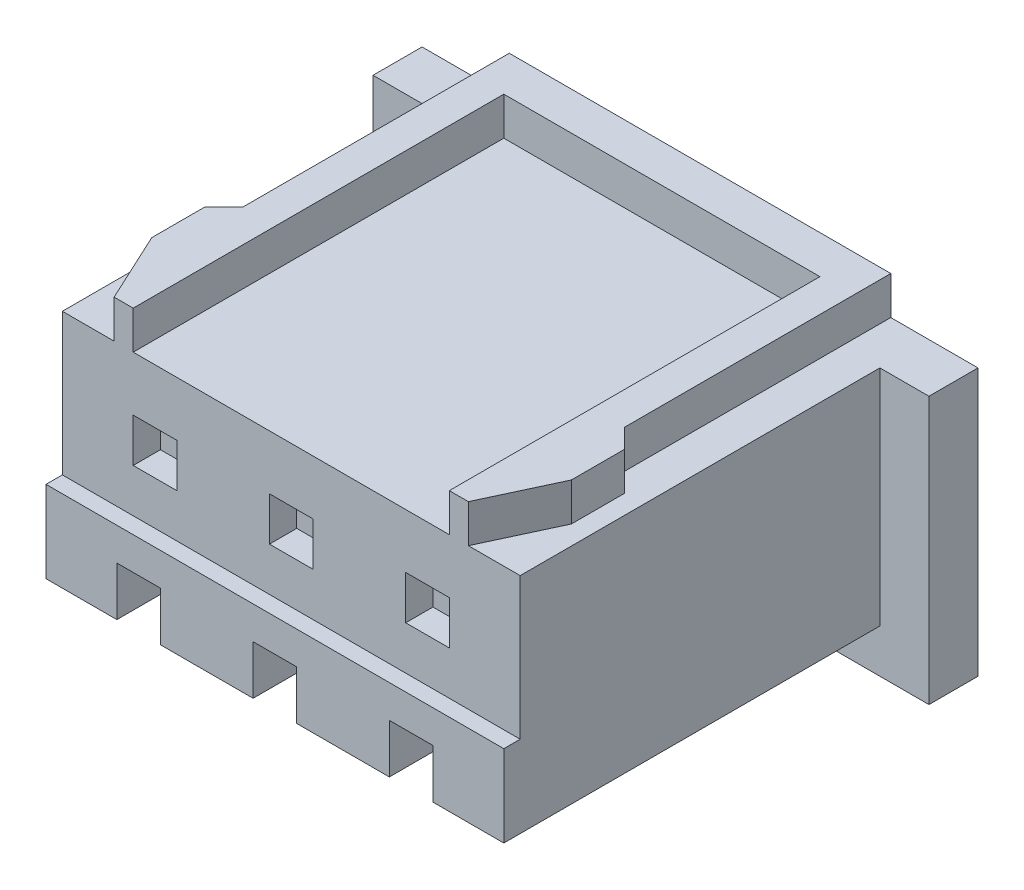
SolidWorks part; units mm, degrees
ref_plane "Plan de face" through (0, 0, 0) normal (0, 0, 1) x (1, 0, 0)
ref_plane "Plan de dessus" through (0, 0, 0) normal (0, 1, 0) x (1, 0, 0)
ref_plane "Plan de droite" through (0, 0, 0) normal (1, 0, 0) x (0, 0, -1)
sketch "Esquisse1" plane through (0, 0, 0) normal (0, 0, 1) x (1, 0, 0)
  line L1 (-5.1, 2.8) -> (5.1, 2.8)
  line L2 (-5.1, 2.8) -> (-5.1, -2.8)
  line L3 (-5.1, -2.8) -> (5.1, -2.8)
  line L4 (5.1, 2.8) -> (5.1, -2.8)
  line L5 (-5.1, 2.8) -> (5.1, -2.8) construction
  line L6 (-5.1, -2.8) -> (5.1, 2.8) construction
  point P0 (0, 0)
  dimension "D1" = 10.2
  dimension "D2" = 5.6
extrude "Boss.-Extru.1" add sketch "Esquisse1" against normal blind 7.8
sketch "Esquisse2" plane through (0, 0, 0) normal (0, 0, 1) x (1, 0, 0)
  line L0 (5.1, -2.8) -> (5.1, 2.8) construction
  line L1 (-5.1, 2.8) -> (5.1, 2.8)
  line L2 (-5.1, 2.8) -> (-5.1, -0.5)
  line L3 (-5.1, -0.5) -> (5.1, -0.5)
  line L4 (5.1, 2.8) -> (5.1, -0.5)
  dimension "D1" = 3.3
extrude "Enlèv. mat.-Extru.1" cut sketch "Esquisse2" against normal blind 0.3
sketch "Esquisse4" plane through (0, 0, 0) normal (0, 0, 1) x (1, 0, 0)
  line L0 (5.1, 2.8) -> (-5.1, 2.8) construction
  line L1 (-5.1, -2.8) -> (5.1, -2.8) construction
  line L2 (5.1, 2.8) -> (-5.1, 2.8)
  line L3 (-5.1, -2.8) -> (5.1, -2.8)
  line L4 (-4.2, 2.8) -> (-4.2, -2)
  line L5 (-4.2, -2) -> (4.2, -2)
  line L6 (4.2, -2) -> (4.2, 2.8)
  line L7 (-5.1, 2.8) -> (-5.1, -0.5) construction
  line L8 (5.1, -0.5) -> (5.1, 2.8) construction
  line L9 (-5.1, -0.5) -> (-5.1, -2.8) construction
  line L10 (5.1, -2.8) -> (5.1, -0.5) construction
  line L11 (-5.1, 2.8) -> (-5.1, -0.5)
  line L12 (-5.1, -0.5) -> (-5.1, -2.8)
  line L13 (5.1, -2.8) -> (5.1, -0.5)
  line L14 (5.1, -0.5) -> (5.1, 2.8)
  line M1 (5.1, -0.5) -> (-5.1, -0.5)
  line M2 (-5.1, -0.5) -> (-5.1, -2.8)
  line M3 (-5.1, -2.8) -> (5.1, -2.8)
  line M4 (5.1, -2.8) -> (5.1, -0.5)
  dimension "D1" = 0.9
  dimension "D2" = 0.9
  dimension "D3" = 0.8
extrude "Enlèv. mat.-Extru.2" cut sketch "Esquisse4" against normal blind 6.9 contours L2 L11 L4 M1 | L6 L5 L4 M1 M2 M3 M4 | L14 L2 L6 M1
sketch "Esquisse5" plane through (0, 2.8, 0) normal (0, 1, 0) x (1, 0, 0)
  line L0 (-3.5, 7.8) -> (-3.5, 2.91)
  line L1 (-3.5, 2.91) -> (-3.85, 2.56)
  line L2 (-3.85, 2.56) -> (-3.85, 1.59)
  line L3 (-3.85, 1.59) -> (-3.25, 0.3)
  line L4 (4.2, 0.3) -> (-4.2, 0.3) construction
  line L5 (-2.9, 0.3) -> (-2.9, 7.1)
  line L6 (-2.9, 7.1) -> (2.9, 7.1)
  line L7 (0, 7.8) -> (0, 0.3) construction
  line L8 (-5.1, 6.9) -> (-4.2, 6.9)
  line L9 (-4.2, 6.9) -> (-4.2, 0.3)
  line L10 (-4.2, 0.3) -> (4.2, 0.3)
  line L11 (4.2, 0.3) -> (4.2, 6.9)
  line L12 (4.2, 6.9) -> (5.1, 6.9)
  line L13 (5.1, 6.9) -> (5.1, 7.8)
  line L14 (5.1, 7.8) -> (-5.1, 7.8)
  line L15 (-5.1, 7.8) -> (-5.1, 6.9)
  line L16 (-5.1, 6.9) -> (-4.2, 6.9)
  line L17 (-4.2, 6.9) -> (-4.2, 0.3)
  line L18 (-4.2, 0.3) -> (4.2, 0.3)
  line L19 (4.2, 0.3) -> (4.2, 6.9)
  line L20 (4.2, 6.9) -> (5.1, 6.9)
  line L21 (5.1, 6.9) -> (5.1, 7.8)
  line L22 (5.1, 7.8) -> (-5.1, 7.8)
  line L23 (-5.1, 7.8) -> (-5.1, 6.9)
  line L24 (5.1, 7.8) -> (5.1, 6.9)
  line L25 (4.2, 6.9) -> (4.2, 0.3)
  line L26 (5.1, 6.9) -> (4.2, 6.9)
  line L27 (2.9, 0.3) -> (2.9, 7.1)
  line L28 (3.85, 1.59) -> (3.25, 0.3)
  line L29 (3.85, 2.56) -> (3.85, 1.59)
  line L30 (3.5, 2.91) -> (3.85, 2.56)
  line L31 (3.5, 7.8) -> (3.5, 2.91)
  point P21 (0, 7.1)
  line M9 (-5.1, 6.9) -> (-4.2, 6.9)
  line M10 (-4.2, 6.9) -> (-4.2, 0.3)
  line M11 (-4.2, 0.3) -> (4.2, 0.3)
  line M12 (4.2, 0.3) -> (4.2, 6.9)
  line M13 (4.2, 6.9) -> (5.1, 6.9)
  line M14 (5.1, 6.9) -> (5.1, 7.8)
  line M15 (5.1, 7.8) -> (-5.1, 7.8)
  line M16 (-5.1, 7.8) -> (-5.1, 6.9)
  dimension "D2" = 0.35
  dimension "D3" = 0.7
  dimension "D4" = 1.29
  dimension "D5" = 0.6
  dimension "D6" = 0.35
  dimension "D7" = 0.97
  dimension "D8" = 0.6
  dimension "D9" = 0.7
  dimension "D1" = 0
extrude "Enlèv. mat.-Extru.3" cut sketch "Esquisse5" against normal blind 0.7 contours L7 L6 L5 M11 | L6 L7 L18 L27 | L31 L30 L29 L28 M15 M11 M12 M13 M14 | L3 L2 L1 L0 M15 M16 M9 M10 M11
sketch "Esquisse6" plane through (0, 0, 0) normal (0, 0, 1) x (1, 0, 0)
  line L0 (-2.9, -2) -> (-2.9, -1.1)
  line L1 (-4.2, -2) -> (4.2, -2) construction
  line L2 (-2.9, -1.1) -> (-2.1, -1.1)
  line L3 (-2.1, -1.1) -> (-2.1, -2)
  line L4 (-4.2, -0.5) -> (-4.2, -2) construction
  line L5 (-0.4, -2) -> (-0.4, -1.1)
  line L6 (-0.4, -1.1) -> (0.4, -1.1)
  line L7 (0.4, -1.1) -> (0.4, -2)
  line L9 (2.1, -2) -> (2.1, -1.1)
  line L10 (2.1, -1.1) -> (2.9, -1.1)
  line L11 (2.9, -1.1) -> (2.9, -2)
  line L13 (-2.9, -2) -> (-2.1, -2)
  line L14 (-0.4, -2) -> (0.4, -2)
  line L15 (2.1, -2) -> (2.9, -2)
  dimension "D1" = 1.3
  dimension "D2" = 0.9
  dimension "D3" = 0.8
  dimension "D4" = 1.7
  dimension "D5" = 1.7
  dimension "D6" = 0.8
  dimension "D7" = 0.8
extrude "Enlèv. mat.-Extru.4" cut sketch "Esquisse6" against normal blind 0.8
sketch "Esquisse7" plane through (0, 0, -0.3) normal (0, 0, 1) x (1, 0, 0)
  line L0 (-2.9, 2.1) -> (2.9, 2.1) construction
  line L1 (-2.9, 1.1) -> (-2.1, 1.1)
  line L2 (-2.9, 1.1) -> (-2.9, 0.3)
  line L3 (-2.9, 0.3) -> (-2.1, 0.3)
  line L4 (-2.1, 1.1) -> (-2.1, 0.3)
  line L5 (-0.4, 1.1) -> (0.4, 1.1)
  line L6 (-0.4, 1.1) -> (-0.4, 0.3)
  line L7 (-0.4, 0.3) -> (0.4, 0.3)
  line L8 (0.4, 1.1) -> (0.4, 0.3)
  line L9 (2.1, 1.1) -> (2.9, 1.1)
  line L10 (2.1, 1.1) -> (2.1, 0.3)
  line L11 (2.1, 0.3) -> (2.9, 0.3)
  line L12 (2.9, 1.1) -> (2.9, 0.3)
  line L13 (-2.9, -1.1) -> (-2.9, -2) construction
  line L14 (-0.4, -1.1) -> (-0.4, -2) construction
  line L15 (2.1, -1.1) -> (2.1, -2) construction
  dimension "D1" = 0.8
  dimension "D2" = 1
extrude "Enlèv. mat.-Extru.5" cut sketch "Esquisse7" against normal blind 0.5
sketch "Esquisse8" plane through (0, 0, -7.8) normal (0, 0, -1) x (-1, 0, 0)
  line L0 (-0.8, 1.5) -> (-0.8, -1.5)
  line L1 (-0.8, 1.5) -> (0.8, 1.5)
  line L2 (0, 1.5) -> (0, 0) construction
  line L3 (-3.5, 2.8) -> (3.5, 2.8) construction
  line L4 (-0.8, -1.5) -> (-0.4, -1.5)
  line L5 (-0.4, -1.5) -> (-0.4, -1.7)
  line L6 (-0.4, -1.7) -> (0.4, -1.7)
  line L7 (0.4, -1.7) -> (0.4, -1.5)
  line L8 (0.4, -1.5) -> (0.8, -1.5)
  line L9 (0.8, -1.5) -> (0.8, 1.5)
  line L10 (0, 0) -> (0, -1.7) construction
  line L11 (-0.7, 0.95) -> (-0.7, -1.45)
  line L12 (-0.7, -1.45) -> (0.7, -1.45)
  line L13 (0.7, -1.45) -> (0.7, 0.95)
  line L14 (0, -1.45) -> (0, 0.95) construction
  line L15 (1.7, 1.5) -> (1.7, -1.5)
  line L16 (1.7, 1.5) -> (3.3, 1.5)
  line L17 (1.7, -1.5) -> (2.1, -1.5)
  line L18 (2.1, -1.5) -> (2.1, -1.7)
  line L19 (2.1, -1.7) -> (2.9, -1.7)
  line L20 (2.9, -1.7) -> (2.9, -1.5)
  line L21 (2.9, -1.5) -> (3.3, -1.5)
  line L22 (3.3, -1.5) -> (3.3, 1.5)
  line L23 (1.8, 0.95) -> (1.8, -1.45)
  line L24 (1.8, -1.45) -> (3.2, -1.45)
  line L25 (3.2, -1.45) -> (3.2, 0.95)
  line L26 (2.5, 1.5) -> (2.5, 0) construction
  line L27 (2.5, 0) -> (2.5, -1.7) construction
  line L28 (2.5, -1.45) -> (2.5, 0.95) construction
  line L29 (-3.3, 1.5) -> (-3.3, -1.5)
  line L30 (-3.3, 1.5) -> (-1.7, 1.5)
  line L31 (-3.3, -1.5) -> (-2.9, -1.5)
  line L32 (-2.9, -1.5) -> (-2.9, -1.7)
  line L33 (-2.9, -1.7) -> (-2.1, -1.7)
  line L34 (-2.1, -1.7) -> (-2.1, -1.5)
  line L35 (-2.1, -1.5) -> (-1.7, -1.5)
  line L36 (-1.7, -1.5) -> (-1.7, 1.5)
  line L37 (-3.2, 0.95) -> (-3.2, -1.45)
  line L38 (-3.2, -1.45) -> (-1.8, -1.45)
  line L39 (-1.8, -1.45) -> (-1.8, 0.95)
  line L40 (-2.5, 1.5) -> (-2.5, 0) construction
  line L41 (-2.5, 0) -> (-2.5, -1.7) construction
  line L42 (-2.5, -1.45) -> (-2.5, 0.95) construction
  arc A0 (-0.7, 0.95) -> (0, 0.95) centre (-0.35, 0.95) cw
  arc A1 (0, 0.95) -> (0.7, 0.95) centre (0.35, 0.95) cw
  arc A2 (1.8, 0.95) -> (2.5, 0.95) centre (2.15, 0.95) cw
  arc A3 (2.5, 0.95) -> (3.2, 0.95) centre (2.85, 0.95) cw
  arc A4 (-3.2, 0.95) -> (-2.5, 0.95) centre (-2.85, 0.95) cw
  arc A5 (-2.5, 0.95) -> (-1.8, 0.95) centre (-2.15, 0.95) cw
  dimension "D1" = 3
  dimension "D2" = 1.6
  dimension "D3" = 1.3
  dimension "D4" = 0.8
  dimension "D5" = 0.2
  dimension "D6" = 0.05
  dimension "D7" = 0.1
  dimension "D8" = 0.1
  dimension "D9" = 2.4
  dimension "D11" = 2.5
  dimension "D13" = 2.5
  dimension "D10" = 2
  dimension "D12" = 2
extrude "Enlèv. mat.-Extru.6" cut sketch "Esquisse8" against normal blind 7 contours L8 L9 L1 L0 L4 L5 L6 L7 A0 A1 L13 L12 L11 | L35 L36 L30 L29 L31 L32 L33 L34 A4 A5 L39 L38 L37 | L21 L22 L16 L15 L17 L18 L19 L20 A2 A3 L25 L24 L23
sketch "Esquisse9" plane through (0, 0, -7.8) normal (0, 0, -1) x (-1, 0, 0)
  line L0 (-0.7, 0.95) -> (-0.7, -1.45) construction
  line L1 (-0.7, -1.45) -> (0.7, -1.45) construction
  line L2 (0.7, -1.45) -> (0.7, 0.95) construction
  line L3 (-3.2, 0.95) -> (-3.2, -1.45) construction
  line L4 (-3.2, -1.45) -> (-1.8, -1.45) construction
  line L5 (-1.8, -1.45) -> (-1.8, 0.95) construction
  line L6 (1.8, 0.95) -> (1.8, -1.45) construction
  line L7 (1.8, -1.45) -> (3.2, -1.45) construction
  line L8 (3.2, -1.45) -> (3.2, 0.95) construction
  line L9 (-0.7, 0.95) -> (-0.7, -1.45)
  line L10 (-0.7, -1.45) -> (0.7, -1.45)
  line L11 (0.7, -1.45) -> (0.7, 0.95)
  line L12 (-3.2, 0.95) -> (-3.2, -1.45)
  line L13 (-3.2, -1.45) -> (-1.8, -1.45)
  line L14 (-1.8, -1.45) -> (-1.8, 0.95)
  line L15 (1.8, 0.95) -> (1.8, -1.45)
  line L16 (1.8, -1.45) -> (3.2, -1.45)
  line L17 (3.2, -1.45) -> (3.2, 0.95)
  arc A0 (0.7, 0.95) -> (0, 0.95) centre (0.35, 0.95) ccw construction
  arc A1 (0, 0.95) -> (-0.7, 0.95) centre (-0.35, 0.95) ccw construction
  arc A2 (-1.8, 0.95) -> (-2.5, 0.95) centre (-2.15, 0.95) ccw construction
  arc A3 (-2.5, 0.95) -> (-3.2, 0.95) centre (-2.85, 0.95) ccw construction
  arc A4 (3.2, 0.95) -> (2.5, 0.95) centre (2.85, 0.95) ccw construction
  arc A5 (2.5, 0.95) -> (1.8, 0.95) centre (2.15, 0.95) ccw construction
  arc A6 (0.7, 0.95) -> (0, 0.95) centre (0.35, 0.95) ccw
  arc A7 (0, 0.95) -> (-0.7, 0.95) centre (-0.35, 0.95) ccw
  arc A8 (-1.8, 0.95) -> (-2.5, 0.95) centre (-2.15, 0.95) ccw
  arc A9 (-2.5, 0.95) -> (-3.2, 0.95) centre (-2.85, 0.95) ccw
  arc A10 (3.2, 0.95) -> (2.5, 0.95) centre (2.85, 0.95) ccw
  arc A11 (2.5, 0.95) -> (1.8, 0.95) centre (2.15, 0.95) ccw
extrude "Enlèv. mat.-Extru.7" cut sketch "Esquisse9" against normal blind 0.8
sketch "Esquisse10" plane through (0, 0, -7) normal (0, 0, -1) x (-1, 0, 0)
  line L0 (0, -1.45) -> (0, 0) construction
  line L1 (-0.7, -1.45) -> (0.7, -1.45) construction
  line L2 (-2.5, 0) -> (0, 0) construction
  line L3 (0, 0) -> (2.5, 0) construction
  line L4 (-2.5, 0) -> (-2.5, -1.45) construction
  line L5 (-3.2, -1.45) -> (-1.8, -1.45) construction
  line L6 (2.5, 0) -> (2.5, -1.45) construction
  line L7 (1.8, -1.45) -> (3.2, -1.45) construction
  circle A0 centre (0, 0) radius 0.6
  circle A1 centre (-2.5, 0) radius 0.6
  circle A2 centre (2.5, 0) radius 0.6
  dimension "D2" = 1.2
  dimension "D1" = 1.45
extrude "Enlèv. mat.-Extru.8" cut sketch "Esquisse10" against normal blind 0.5
sketch "Esquisse11" plane through (0, 0, -0.8) normal (0, 0, 1) x (1, 0, 0)
  line L0 (-2.1, -2) -> (-2.1, -1.7) construction
  line L1 (-2.1, -1.7) -> (-2.9, -1.7) construction
  line L2 (-2.9, -1.7) -> (-2.9, -2) construction
  line L3 (-2.9, -2) -> (-2.1, -2) construction
  line L4 (0.4, -2) -> (0.4, -1.7) construction
  line L5 (0.4, -1.7) -> (-0.4, -1.7) construction
  line L6 (-0.4, -1.7) -> (-0.4, -2) construction
  line L7 (-0.4, -2) -> (0.4, -2) construction
  line L8 (2.9, -1.7) -> (2.1, -1.7) construction
  line L9 (2.1, -1.7) -> (2.1, -2) construction
  line L10 (2.1, -2) -> (2.9, -2) construction
  line L11 (2.9, -2) -> (2.9, -1.7) construction
  line L12 (-2.1, -2) -> (-2.1, -1.7)
  line L13 (-2.1, -1.7) -> (-2.9, -1.7)
  line L14 (-2.9, -1.7) -> (-2.9, -2)
  line L15 (-2.9, -2) -> (-2.1, -2)
  line L16 (0.4, -2) -> (0.4, -1.7)
  line L17 (0.4, -1.7) -> (-0.4, -1.7)
  line L18 (-0.4, -1.7) -> (-0.4, -2)
  line L19 (-0.4, -2) -> (0.4, -2)
  line L20 (2.9, -1.7) -> (2.1, -1.7)
  line L21 (2.1, -1.7) -> (2.1, -2)
  line L22 (2.1, -2) -> (2.9, -2)
  line L23 (2.9, -2) -> (2.9, -1.7)
extrude "Enlèv. mat.-Extru.9" cut sketch "Esquisse11" against normal blind 2.2
